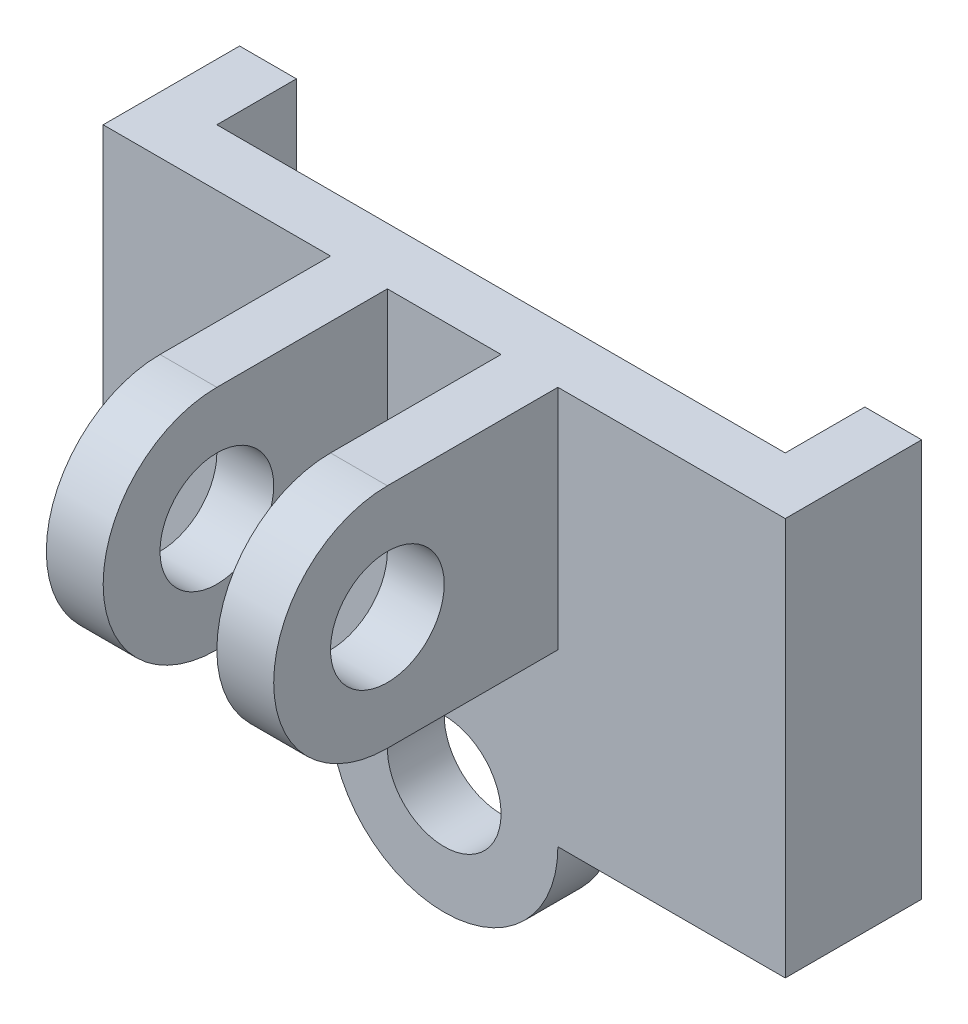
SolidWorks part; units mm, degrees
ref_plane "Plane1" through (0, 0, 0) normal (0, 0, 1) x (1, 0, 0)
ref_plane "Plane2" through (0, 0, 0) normal (0, 1, 0) x (1, 0, 0)
ref_plane "Plane3" through (0, 0, 0) normal (1, 0, 0) x (0, 0, -1)
sketch "Sketch1" plane through (0, 0, 0) normal (0, 0, 1) x (1, 0, 0)
  line L0 (0, 0) -> (20, 0)
  line L1 (40, 0) -> (60, 0)
  line L2 (60, 0) -> (60, 35)
  line L3 (60, 35) -> (0, 35)
  line L4 (0, 35) -> (0, 0)
  arc A0 (40, 0) -> (20, 0) centre (30, 0) cw
extrude "Base-Extrude" add sketch "Sketch1" along normal blind 12
sketch "Sketch2" plane through (0, 0, 12) normal (0, 0, 1) x (1, 0, 0)
  circle A0 centre (30, 0) radius 5
extrude "Cut-Extrude1" cut sketch "Sketch2" against normal blind 12
sketch "Sketch3" plane through (0, 35, 0) normal (0, 1, 0) x (-1, 0, 0)
  line L0 (-60, 0) -> (0, 0) construction
  line L1 (-55, 0) -> (-5, 0)
  line L2 (-55, 0) -> (-55, 7)
  line L3 (-55, 7) -> (-5, 7)
  line L4 (-5, 0) -> (-5, 7)
extrude "Cut-Extrude2" cut sketch "Sketch3" against normal blind 60
sketch "Sketch4" plane through (0, 0, 12) normal (0, 0, 1) x (1, 0, 0)
  line L0 (60, 35) -> (0, 35) construction
  line L1 (20, 35) -> (25, 35)
  line L2 (20, 35) -> (20, 15)
  line L3 (20, 15) -> (25, 15)
  line L4 (25, 35) -> (25, 15)
  line L6 (35, 35) -> (40, 35)
  line L7 (35, 35) -> (35, 15)
  line L8 (35, 15) -> (40, 15)
  line L9 (40, 35) -> (40, 15)
extrude "Boss-Extrude1" add sketch "Sketch4" along normal blind 15
sketch "Sketch5" plane through (40, 0, 0) normal (1, 0, 0) x (0, 0, -1)
  line L0 (-27, 35) -> (-27, 21)
  line L1 (-27, 15) -> (-27, 35) construction
  line L2 (-27, 21) -> (-27, 15)
  arc A0 (-27, 35) -> (-27, 15) centre (-27, 25) ccw
extrude "Boss-Extrude2" add sketch "Sketch5" against normal blind 5
sketch "Sketch6" plane through (20, 0, 0) normal (-1, 0, 0) x (0, 0, 1)
  line L0 (27, 35) -> (27, 15)
  arc A0 (27, 35) -> (27, 15) centre (27, 25) cw
extrude "Boss-Extrude3" add sketch "Sketch6" against normal blind 5
sketch "Sketch7" plane through (40, 0, 0) normal (1, 0, 0) x (0, 0, -1)
  circle A0 centre (-27, 25) radius 5
extrude "Cut-Extrude3" cut sketch "Sketch7" against normal blind 40
